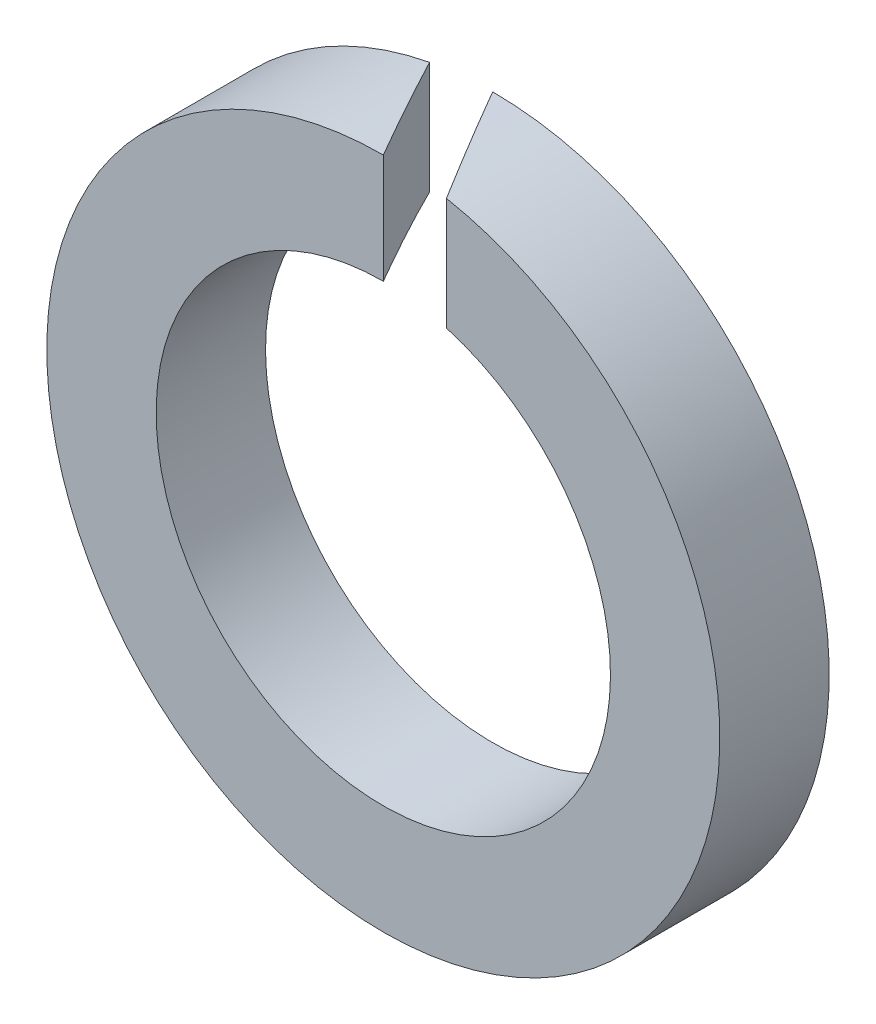
SolidWorks part; units mm, degrees
ref_plane "Front" through (0, 0, 0) normal (0, 0, 1) x (1, 0, 0)
ref_plane "Top" through (0, 0, 0) normal (0, 1, 0) x (1, 0, 0)
ref_plane "Right" through (0, 0, 0) normal (1, 0, 0) x (0, 0, -1)
sketch "Sketch1" plane through (0, 0, 0) normal (0, 0, 1) x (1, 0, 0)
  circle A0 centre (0, 0) radius 2.7
  circle A1 centre (0, 0) radius 4
  dimension "d" = 5.4
  dimension "b" = 1.3
extrude "Base-Extrude" add sketch "Sketch1" against normal blind 1.3
sketch "Sketch2" plane through (0, 0, 0) normal (0, 1, 0) x (1, 0, 0)
  line L0 (0, 1.3) -> (0.7506, 0)
  line L1 (0.7506, 0) -> (0, 0)
  line L3 (0, 0) -> (-0.7506, 1.3)
  line L5 (-0.7506, 1.3) -> (0, 1.3)
  line L7 (4, 1.3) -> (-4, 1.3) construction
  dimension "m" = 0.65
extrude "Cut-Extrude1" cut sketch "Sketch2" along normal through all
